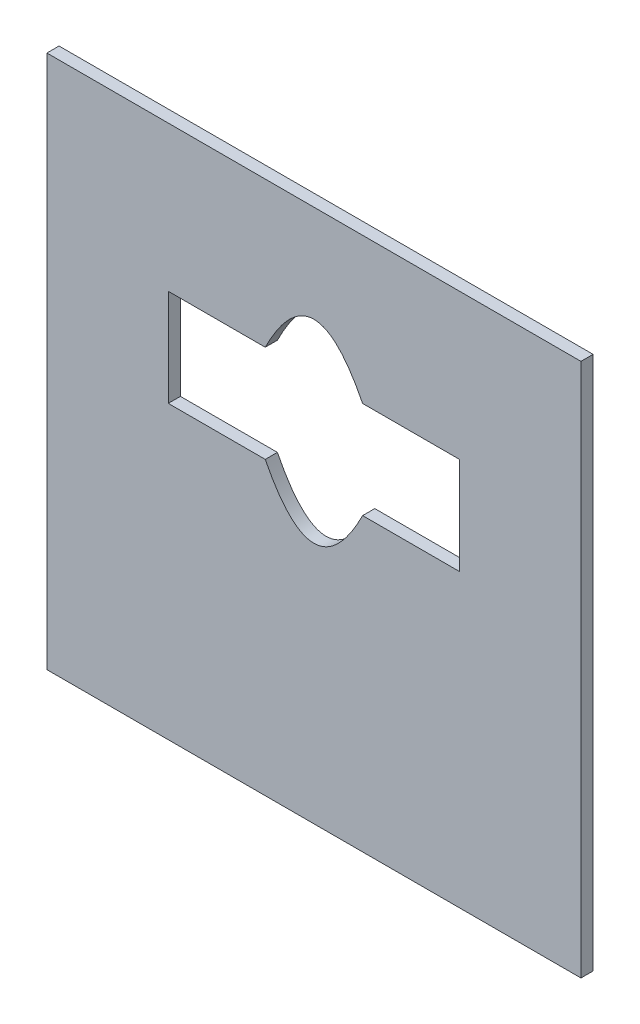
SolidWorks part; units mm, degrees
ref_plane "Front Plane" through (0, 0, 0) normal (0, 0, 1) x (1, 0, 0)
ref_plane "Top Plane" through (0, 0, 0) normal (0, 1, 0) x (1, 0, 0)
ref_plane "Right Plane" through (0, 0, 0) normal (1, 0, 0) x (0, 0, -1)
sketch "Sketch1" plane through (0, 0, 0) normal (0, 0, 1) x (1, 0, 0)
  line L0 (31.75, 101.6) -> (57.1143, 101.6)
  line L1 (0, 0) -> (139.7, 0)
  line L2 (0, 0) -> (0, 139.7)
  line L3 (0, 139.7) -> (139.7, 139.7)
  line L4 (139.7, 0) -> (139.7, 139.7)
  line L5 (82.5857, 101.6) -> (107.95, 101.6)
  line L6 (31.75, 101.6) -> (31.75, 76.2)
  line L7 (31.75, 76.2) -> (57.1143, 76.2)
  line L8 (107.95, 101.6) -> (107.95, 76.2)
  line L9 (82.5857, 76.2) -> (107.95, 76.2)
  spline S0 degree 2 poles (57.1143, 101.6) (69.85, 127) (82.5857, 101.6) knots 0 0 0 1 1 1
  spline S1 degree 2 poles (57.1143, 76.2) (69.85, 50.9177) (82.5857, 76.2) knots 0 0 0 1 1 1
extrude "Boss-Extrude1" add sketch "Sketch1" along normal blind 3.175
